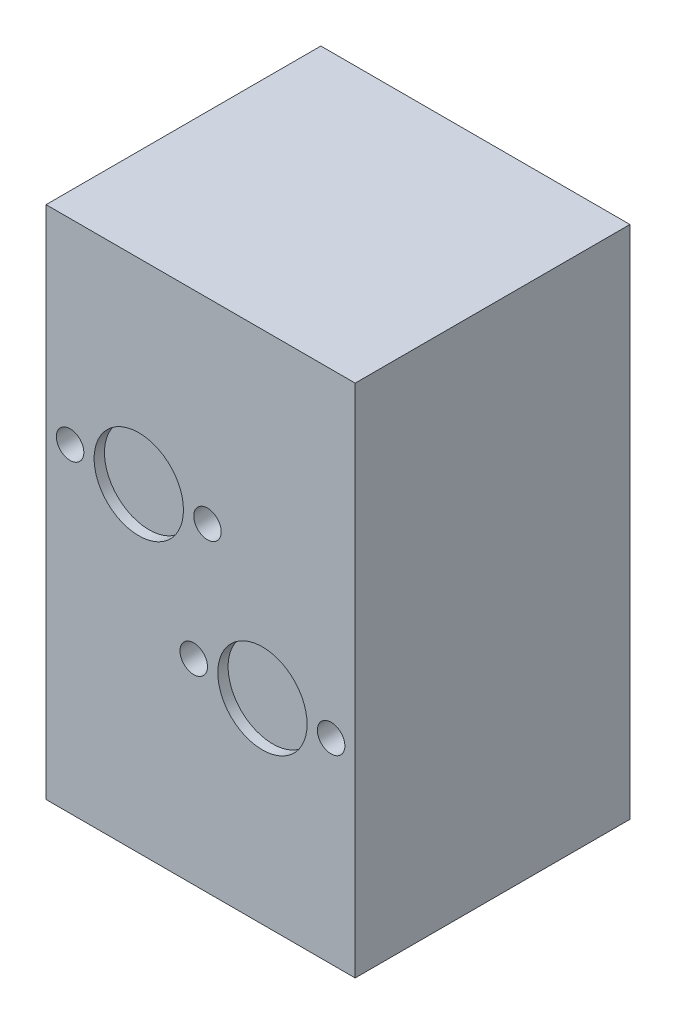
SolidWorks part; units mm, degrees
ref_plane "前视基准面" through (0, 0, 0) normal (0, 0, 1) x (1, 0, 0)
ref_plane "上视基准面" through (0, 0, 0) normal (0, 1, 0) x (1, 0, 0)
ref_plane "右视基准面" through (0, 0, 0) normal (1, 0, 0) x (0, 0, -1)
sketch "草图1" plane through (0, 0, 0) normal (0, 0, 1) x (1, 0, 0)
  line L1 (-45, 75) -> (45, 75)
  line L2 (-45, 75) -> (-45, -75)
  line L3 (-45, -75) -> (45, -75)
  line L4 (45, 75) -> (45, -75)
  line L5 (-45, 75) -> (45, -75) construction
  line L6 (-45, -75) -> (45, 75) construction
  point P0 (0, 0)
  dimension "D1" = 90
  dimension "D2" = 150
extrude "凸台-拉伸1" add sketch "草图1" along normal blind 80
sketch "草图2" plane through (0, 0, 80) normal (0, 0, 1) x (1, 0, 0)
  circle A1 centre (18, -18) radius 13
  circle A2 centre (-18, 18) radius 13
  dimension "D1" = 36
  dimension "D2" = 36
  dimension "D5" = 26
  dimension "D6" = 26
  dimension "D3" = 18
  dimension "D4" = 18
extrude "切除-拉伸1" cut sketch "草图2" against normal blind 3
sketch "草图3" plane through (0, 0, 80) normal (0, 0, 1) x (1, 0, 0)
  circle A0 centre (2, 18) radius 4
  circle A1 centre (-38, 18) radius 4
  circle A2 centre (-18, 18) radius 13 construction
  circle A3 centre (-2, -18) radius 4
  circle A4 centre (38, -18) radius 4
  dimension "D1" = 8
  dimension "D2" = 8
  dimension "D3" = 40
  dimension "D4" = 20
  dimension "D5" = 2
extrude "切除-拉伸2" cut sketch "草图3" against normal blind 10
sketch "草图4" plane through (0, 0, 0) normal (0, 0, -1) x (-1, 0, 0)
  circle A0 centre (-19.5, 60.373) radius 4
  circle A1 centre (-19.5, -34.627) radius 4
  circle A2 centre (19.5, -34.627) radius 4
  circle A3 centre (-19.5, 34.627) radius 4
  circle A4 centre (-19.5, -60.373) radius 4
  circle A5 centre (19.5, -60.373) radius 4
  circle A6 centre (19.5, 34.627) radius 4
  circle A7 centre (19.5, 60.373) radius 4
  arc A8 (-25.975, 55.6746) -> (-12.5, 56.5) centre (-19.5, 60.373) ccw construction
  arc A9 (12.5, 56.5) -> (25.975, 55.6746) centre (19.5, 60.373) ccw construction
  arc A10 (-25.975, -39.3254) -> (-12.5, -38.5) centre (-19.5, -34.627) ccw construction
  arc A11 (12.5, -38.5) -> (25.975, -39.3254) centre (19.5, -34.627) ccw construction
  arc A12 (25.975, 39.3254) -> (12.5, 38.5) centre (19.5, 34.627) ccw construction
  arc A13 (-12.5, 38.5) -> (-25.975, 39.3254) centre (-19.5, 34.627) ccw construction
  arc A14 (25.975, -55.6746) -> (12.5, -56.5) centre (19.5, -60.373) ccw construction
  arc A15 (-12.5, -56.5) -> (-25.975, -55.6746) centre (-19.5, -60.373) ccw construction
  dimension "D1" = 8
  dimension "D2" = 8
  dimension "D3" = 8
  dimension "D4" = 8
  dimension "D5" = 8
  dimension "D6" = 8
  dimension "D7" = 8
  dimension "D8" = 8
extrude "切除-拉伸3" cut sketch "草图4" against normal blind 7
